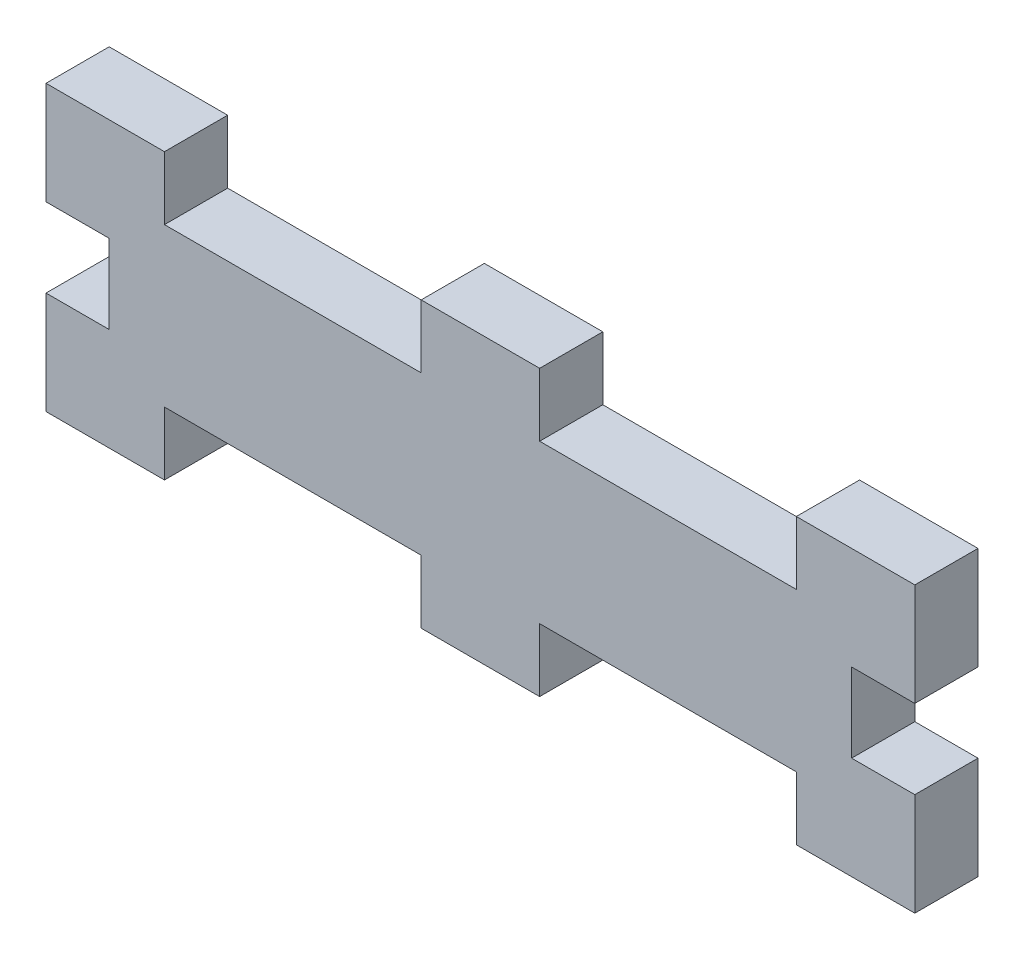
SolidWorks part; units mm, degrees
ref_plane "Front" through (0, 0, 0) normal (0, 0, 1) x (1, 0, 0)
ref_plane "Top" through (0, 0, 0) normal (0, 1, 0) x (1, 0, 0)
ref_plane "Right" through (0, 0, 0) normal (1, 0, 0) x (0, 0, -1)
sketch "Sketch1" plane through (0, 0, 0) normal (0, 0, 1) x (1, 0, 0)
  line L1 (-34.925, 6.35) -> (34.925, 6.35)
  line L2 (-34.925, 6.35) -> (-34.925, -6.35)
  line L3 (-34.925, -6.35) -> (34.925, -6.35)
  line L4 (34.925, 6.35) -> (34.925, -6.35)
  line L5 (-34.925, 6.35) -> (34.925, -6.35) construction
  line L6 (-34.925, -6.35) -> (34.925, 6.35) construction
  point P0 (0, 0)
  dimension "D1" = 12.7
  dimension "D2" = 69.85
extrude "Boss-Extrude1" add sketch "Sketch1" along normal blind 5.08
sketch "Sketch2" plane through (0, 0, 5.08) normal (0, 0, 1) x (1, 0, 0)
  line L0 (34.925, 6.35) -> (-34.925, 6.35) construction
  line L1 (-34.925, 6.35) -> (-25.4, 6.35)
  line L2 (-34.925, 6.35) -> (-34.925, 11.43)
  line L3 (-34.925, 11.43) -> (-25.4, 11.43)
  line L4 (-25.4, 6.35) -> (-25.4, 11.43)
  line L5 (34.925, 6.35) -> (25.4, 6.35)
  line L6 (34.925, 6.35) -> (34.925, 11.43)
  line L7 (34.925, 11.43) -> (25.4, 11.43)
  line L8 (25.4, 6.35) -> (25.4, 11.43)
  line L9 (4.7625, 11.43) -> (-4.7625, 11.43)
  line L10 (4.7625, 11.43) -> (4.7625, 6.35)
  line L11 (4.7625, 6.35) -> (-4.7625, 6.35)
  line L12 (-4.7625, 11.43) -> (-4.7625, 6.35)
  line L13 (4.7625, 11.43) -> (-4.7625, 6.35) construction
  line L14 (4.7625, 6.35) -> (-4.7625, 11.43) construction
  point P10 (0, 8.89)
  point P17 (0, 0)
  dimension "D1" = 5.08
  dimension "D2" = 9.525
extrude "Boss-Extrude2" add sketch "Sketch2" against normal blind 5.08
mirror "Mirror1" about plane through (0, 0, 0) normal (0, 1, 0) of "Boss-Extrude2"
sketch "Sketch3" plane through (0, 0, 5.08) normal (0, 0, 1) x (1, 0, 0)
  line L0 (-34.925, 11.43) -> (-34.925, -11.43) construction
  line L1 (-29.845, -3.175) -> (-34.925, -3.175)
  line L2 (-29.845, -3.175) -> (-29.845, 3.175)
  line L3 (-29.845, 3.175) -> (-34.925, 3.175)
  line L4 (-34.925, -3.175) -> (-34.925, 3.175)
  line L5 (-29.845, -3.175) -> (-34.925, 3.175) construction
  line L6 (-29.845, 3.175) -> (-34.925, -3.175) construction
  line L7 (34.925, -11.43) -> (34.925, 11.43) construction
  line L8 (29.845, -3.175) -> (34.925, -3.175)
  line L9 (29.845, -3.175) -> (29.845, 3.175)
  line L10 (29.845, 3.175) -> (34.925, 3.175)
  line L11 (34.925, -3.175) -> (34.925, 3.175)
  line L12 (29.845, -3.175) -> (34.925, 3.175) construction
  line L13 (29.845, 3.175) -> (34.925, -3.175) construction
  point P0 (-32.385, 0)
  point P7 (32.385, 0)
  point P14 (0, 0)
  dimension "D1" = 6.35
  dimension "D2" = 5.08
extrude "Cut-Extrude1" cut sketch "Sketch3" against normal blind 5.08
